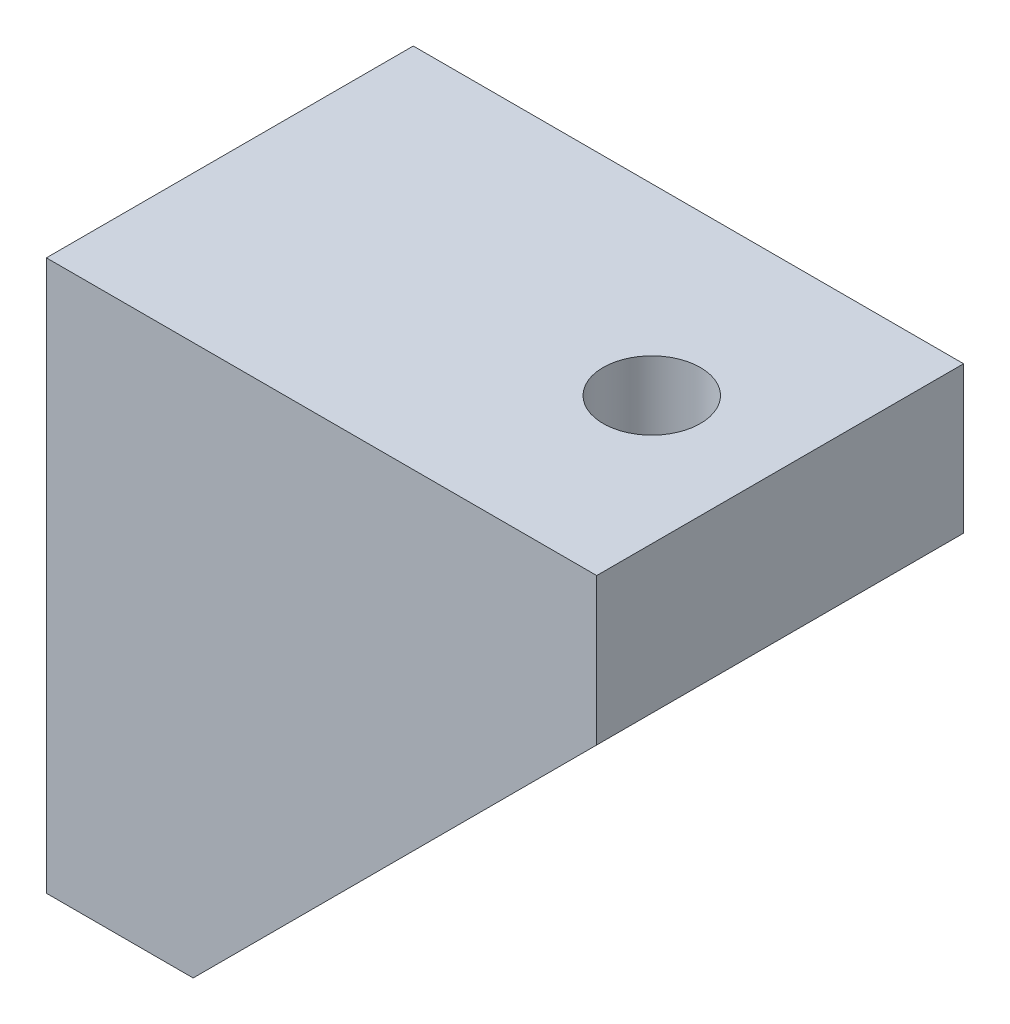
SolidWorks part; units mm, degrees
ref_plane "Front Plane" through (0, 0, 0) normal (0, 0, 1) x (1, 0, 0)
ref_plane "Top Plane" through (0, 0, 0) normal (0, 1, 0) x (1, 0, 0)
ref_plane "Right Plane" through (0, 0, 0) normal (1, 0, 0) x (0, 0, -1)
sketch "Sketch1" plane through (0, 0, 0) normal (0, 0, 1) x (1, 0, 0)
  line L0 (0, 0) -> (0, 30)
  line L1 (0, 30) -> (30, 30)
  line L2 (30, 30) -> (30, 22)
  line L3 (30, 22) -> (8, 0)
  line L4 (8, 0) -> (0, 0)
  dimension "D1" = 8
  dimension "D2" = 30
extrude "Boss-Extrude1" add sketch "Sketch1" along normal blind 4
sketch "Sketch2" plane through (0, 0, 4) normal (0, 0, 1) x (1, 0, 0)
  line L0 (0, 0) -> (8, 0)
  line L1 (8, 0) -> (8, 22)
  line L2 (8, 22) -> (30, 22)
  line L3 (30, 22) -> (30, 30)
  line L4 (30, 30) -> (0, 30)
  line L5 (0, 30) -> (0, 0)
extrude "Boss-Extrude2" add sketch "Sketch2" along normal blind 12
sketch "Sketch3" plane through (0, 0, 16) normal (0, 0, 1) x (1, 0, 0)
  line L0 (0, 30) -> (0, 0) construction
  line L1 (0, 0) -> (8, 0) construction
  line L4 (30, 22) -> (30, 30) construction
  line L5 (30, 30) -> (0, 30) construction
  line L8 (8, 0) -> (30, 22) construction
  line L9 (0, 30) -> (0, 0)
  line L10 (0, 0) -> (8, 0)
  line L13 (30, 22) -> (30, 30)
  line L14 (30, 30) -> (0, 30)
  line L17 (8, 0) -> (30, 22)
extrude "Boss-Extrude3" add sketch "Sketch3" along normal blind 4
sketch "Sketch4" plane through (8, 0, 0) normal (1, 0, 0) x (0, 0, -1)
  line L0 (-10, 22) -> (-10, 0) construction
  line L1 (-16, 22) -> (-4, 22) construction
  line L2 (-16, 0) -> (-4, 0) construction
  circle A0 centre (-10, 11) radius 2.65
  dimension "D1" = 5.3
extrude "Cut-Extrude1" cut sketch "Sketch4" against normal up to vertex (8 mm away) up to point (0, 0, 20)
sketch "Sketch5" plane through (0, 22, 0) normal (0, -1, 0) x (1, 0, 0)
  line L0 (8, 10) -> (30, 10) construction
  line L1 (8, 16) -> (8, 4) construction
  line L2 (30, 16) -> (30, 4) construction
  circle A0 centre (23, 10) radius 2.65
  dimension "D2" = 5.3
  dimension "D1" = 15
extrude "Cut-Extrude2" cut sketch "Sketch5" against normal up to vertex (8 mm away) up to point (30, 30, 20)
